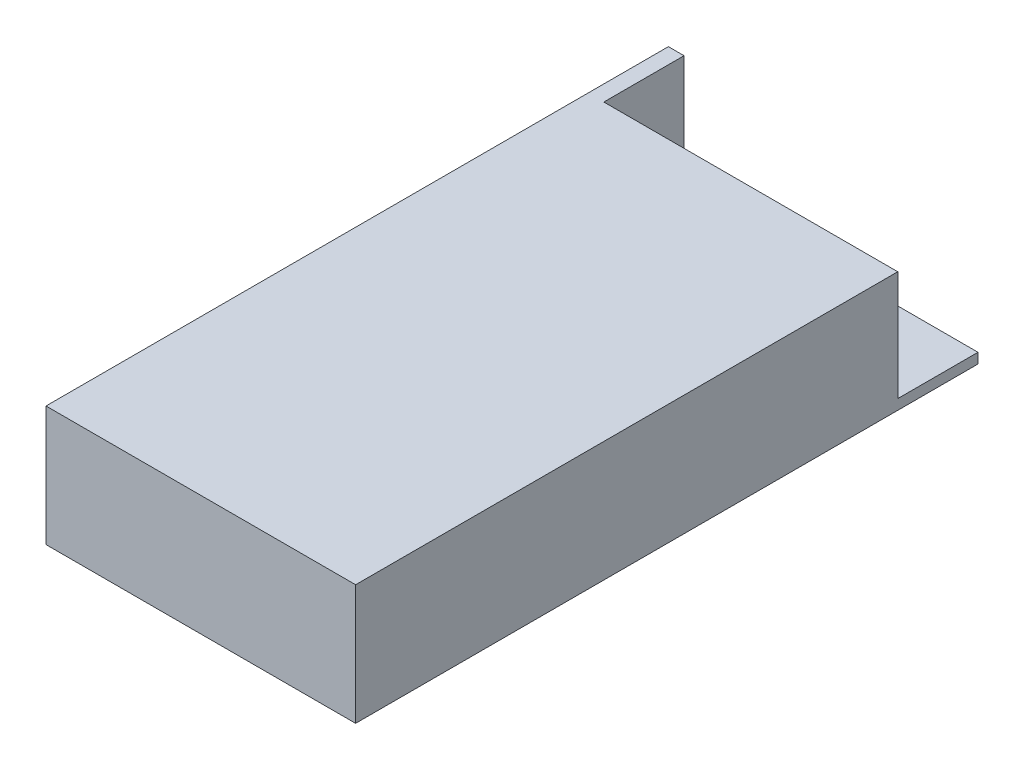
SolidWorks part; units mm, degrees
ref_plane "Front" through (0, 0, 0) normal (0, 0, 1) x (1, 0, 0)
ref_plane "Top" through (0, 0, 0) normal (0, 1, 0) x (1, 0, 0)
ref_plane "Right" through (0, 0, 0) normal (1, 0, 0) x (0, 0, -1)
sketch "Sketch1" plane through (0, 0, 0) normal (0, 1, 0) x (1, 0, 0)
  line L1 (-49, -98.5) -> (49, -98.5)
  line L2 (-49, -98.5) -> (-49, 98.5)
  line L3 (-49, 98.5) -> (49, 98.5)
  line L4 (49, -98.5) -> (49, 98.5)
  line L5 (-49, -98.5) -> (49, 98.5) construction
  line L6 (-49, 98.5) -> (49, -98.5) construction
  point P0 (0, 0)
  dimension "D1" = 98
  dimension "D2" = 197
extrude "Boss-Extrude1" add sketch "Sketch1" along normal mid plane 38
hole_wizard "M3x0.5 Tapped Hole1" positions "Sketch5" profile "Sketch4" tap size "M3x0.5" standard "Ansi Metric"
sketch "Sketch5" plane through (0, -19, 0) normal (0, -1, 0) x (1, 0, 0)
  line L1 (38.5901, -36.5) -> (-40, -36.5) construction
  line L3 (40, 83.5) -> (-40, 83.5) construction
  line L7 (49, -98.5) -> (-49, -98.5) construction
  point P0 (-40, -36.5)
  point P1 (40, -36.5)
  point P3 (-40, 83.5)
  point P5 (40, 83.5)
  dimension "D1" = 80
  dimension "D2" = 120
  dimension "D3" = 62
  dimension "D4" = 40
sketch "Sketch4" plane through (-40, -19, -36.5) normal (1, 0, 0) x (0, 0, -1)
  line L0 (0, 0) -> (0, 8.2441)
  line L1 (0, 8.2441) -> (1.25, 7.493)
  line L2 (1.25, 7.493) -> (1.25, 5.9944)
  line L3 (1.25, 5.9944) -> (1.5, 5.9944)
  line L4 (1.5, 5.9944) -> (1.5, 0)
  line L5 (1.5, 0) -> (0, 0)
  line L10 (0, 8.2441) -> (-1.25, 7.493) construction
  line L11 (0, -6.35) -> (0, 107.95) construction
  dimension "Tap Drill Dia." = 2.5
  dimension "Tap Drill Depth" = 7.493
  dimension "Thread Major Dia." = 3
  dimension "Thread Depth" = 5.9944
  dimension "Drill Angle" = 118
sketch "Sketch6" plane through (0, 0, -98.5) normal (0, 0, -1) x (-1, 0, 0)
  line L1 (-49, 19) -> (44.0379, 19)
  line L2 (-49, 19) -> (-49, -15.7773)
  line L3 (-49, -15.7773) -> (44.0379, -15.7773)
  line L4 (44.0379, 19) -> (44.0379, -15.7773)
extrude "Cut-Extrude2" cut sketch "Sketch6" against normal blind 25.4
sketch "Sketch3" plane through (0, 0, -73.1) normal (0, 0, -1) x (-1, 0, 0)
  text T0 "OUTPUTS"
extrude "Cut-Extrude1" cut sketch "Sketch3" against normal blind 0.1016
